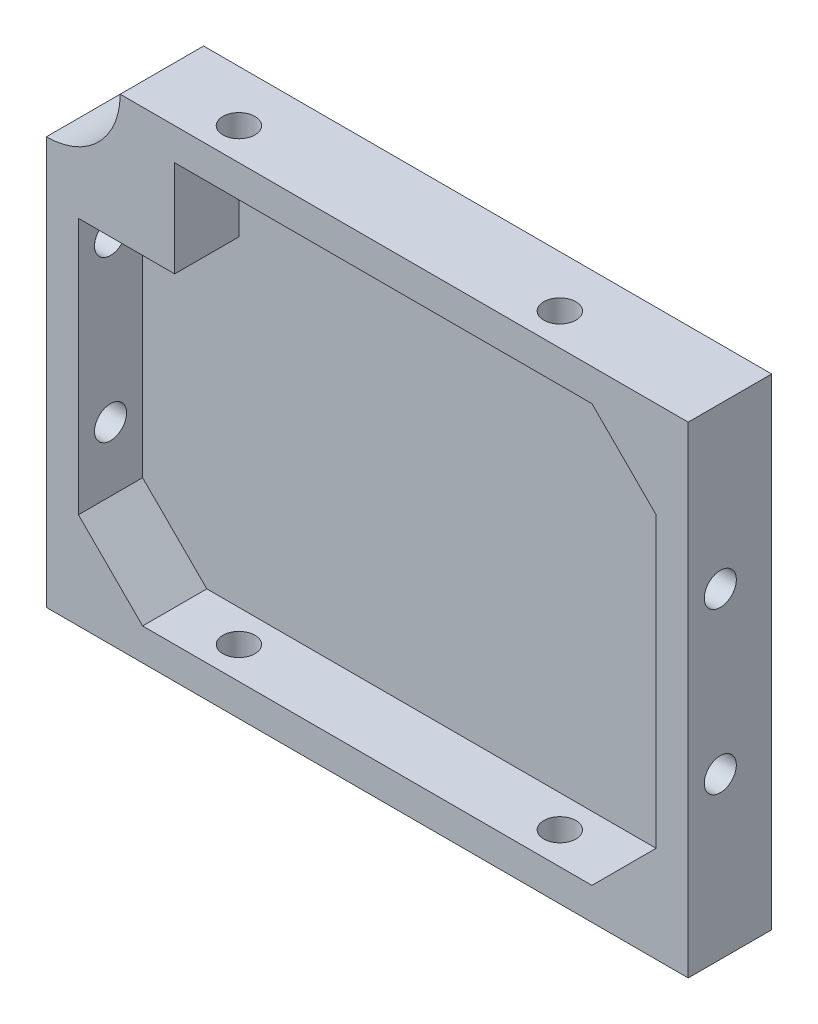
SolidWorks part; units mm, degrees
ref_plane "Plan de face" through (0, 0, 0) normal (0, 0, 1) x (1, 0, 0)
ref_plane "Plan de dessus" through (0, 0, 0) normal (0, 1, 0) x (1, 0, 0)
ref_plane "Plan de droite" through (0, 0, 0) normal (1, 0, 0) x (0, 0, -1)
sketch "Esquisse1" plane through (0, 0, 0) normal (0, 0, 1) x (1, 0, 0)
  line L0 (44.1184, 33.7284) -> (54.1184, 33.7284)
  line L1 (-45.8816, 33.7284) -> (44.1184, 33.7284)
  line L2 (-45.8816, 33.7284) -> (-45.8816, -41.2716)
  line L3 (-45.8816, -41.2716) -> (54.1184, -41.2716)
  line L4 (54.1184, 23.7284) -> (54.1184, -41.2716)
  line L5 (54.1184, 33.7284) -> (54.1184, 23.7284)
  point P6 (54.1184, 33.7284)
  dimension "D1" = 100
  dimension "D2" = 75
extrude "Boss.-Extru.1" add sketch "Esquisse1" along normal blind 13
shell "Coque1" thickness 5
sketch "Esquisse2" plane through (-45.8816, 0, 0) normal (-1, 0, 0) x (0, 0, 1)
  line L0 (13, 33.7284) -> (13, -41.2716) construction
  line L1 (13, 33.7284) -> (0, 33.7284) construction
  line L2 (13, -41.2716) -> (0, -41.2716) construction
  circle A0 centre (8, 8.7284) radius 2.5
  circle A1 centre (8, -16.2716) radius 2.5
  dimension "D1" = 5
  dimension "D2" = 5
  dimension "D3" = 5
  dimension "D4" = 5
  dimension "D5" = 25
  dimension "D6" = 25
extrude "Enlèv. mat.-Extru.1" cut sketch "Esquisse2" against normal up to surface (100 mm away) contours A1 | A0 up to face at (54.1184, -3.7716, 6.5)
sketch "Esquisse3" plane through (0, -41.2716, 0) normal (0, -1, 0) x (1, 0, 0)
  line L0 (-45.8816, 13) -> (54.1184, 13) construction
  line L2 (54.1184, 13) -> (54.1184, 0) construction
  line L3 (-45.8816, 13) -> (-45.8816, 0) construction
  circle A0 centre (-20.8816, 8) radius 2.5
  circle A1 centre (29.1184, 8) radius 2.5
  dimension "D1" = 5
  dimension "D2" = 5
  dimension "D3" = 5
  dimension "D4" = 5
  dimension "D5" = 25
  dimension "D6" = 25
extrude "Enlèv. mat.-Extru.2" cut sketch "Esquisse3" against normal up to surface (75 mm away) up to face at (4.1184, 33.7284, 6.5)
sketch "Esquisse4" plane through (0, 0, 3) normal (0, 0, 1) x (1, 0, 0)
  line L0 (-30.8816, -36.2716) -> (-40.8816, -26.2716)
  line L1 (49.1184, 28.7284) -> (-40.8816, 28.7284) construction
  line L3 (-40.8816, 28.7284) -> (-40.8816, -36.2716) construction
  line L4 (-40.8816, -26.2716) -> (-40.8816, -36.2716)
  line L5 (49.1184, 28.7284) -> (49.1184, 18.7284)
  line L6 (49.1184, -36.2716) -> (49.1184, 28.7284) construction
  line L7 (49.1184, 18.7284) -> (39.1184, 28.7284)
  line L8 (39.1184, 28.7284) -> (49.1184, 28.7284)
  line L9 (49.1184, 28.7284) -> (-40.8816, 28.7284) construction
  line L10 (49.1184, -36.2716) -> (49.1184, -26.2716)
  line L11 (49.1184, -26.2716) -> (39.1184, -36.2716)
  line L12 (-40.8816, -36.2716) -> (49.1184, -36.2716) construction
  line L13 (39.1184, -36.2716) -> (49.1184, -36.2716)
  line L14 (-40.8816, 28.7284) -> (-40.8816, -36.2716) construction
  line L15 (-40.8816, -36.2716) -> (-30.8816, -36.2716)
  line L17 (-25.8816, 28.7284) -> (-25.8816, 13.7284)
  line L18 (-25.8816, 13.7284) -> (-40.8816, 13.7284)
  line L19 (-40.8816, 13.7284) -> (-40.8816, 28.7284)
  line L20 (-40.8816, 28.7284) -> (-25.8816, 28.7284)
  dimension "D1" = 10
  dimension "D2" = 10
  dimension "D3" = 10
  dimension "D4" = 10
  dimension "D5" = 10
  dimension "D6" = 10
  dimension "D7" = 15
  dimension "D8" = 15
extrude "Boss.-Extru.2" add sketch "Esquisse4" along normal up to surface (10 mm away) up to face at (4.1184, -3.7716, 13)
sketch "Esquisse6" plane through (0, 0, 13) normal (0, 0, 1) x (1, 0, 0)
  circle A0 centre (-45.8816, 33.7284) radius 11.5
  dimension "D1" = 23
extrude "Enlèv. mat.-Extru.4" cut sketch "Esquisse6" against normal up to surface (13 mm away) up to face at (4.1184, -3.7716, 0)
